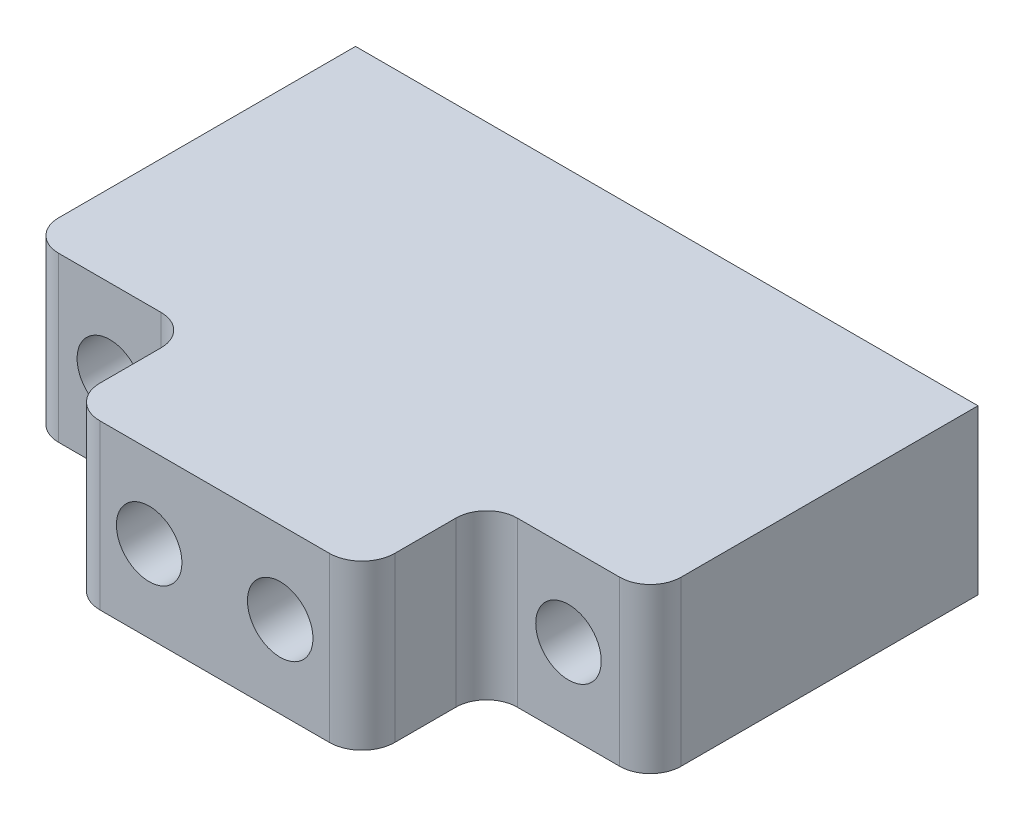
SolidWorks part; units mm, degrees
ref_plane "Front Plane" through (0, 0, 0) normal (0, 0, 1) x (1, 0, 0)
ref_plane "Top Plane" through (0, 0, 0) normal (0, 1, 0) x (1, 0, 0)
ref_plane "Right Plane" through (0, 0, 0) normal (1, 0, 0) x (0, 0, -1)
sketch "Sketch1" plane through (0, 0, 0) normal (0, 0, 1) x (1, 0, 0)
  line L0 (-24.13, 0) -> (-17.78, 0) construction
  line L1 (-24.13, 6.35) -> (24.13, 6.35)
  line L2 (-24.13, 6.35) -> (-24.13, -6.35)
  line L3 (-24.13, -6.35) -> (24.13, -6.35)
  line L4 (24.13, 6.35) -> (24.13, -6.35)
  line L5 (-24.13, 6.35) -> (24.13, -6.35) construction
  line L6 (-24.13, -6.35) -> (24.13, 6.35) construction
  circle A0 centre (-17.78, 0) radius 2.54
  point P0 (0, 0)
  dimension "D3" = 6.35
  dimension "D1" = 48.26
  dimension "D2" = 12.7
extrude "Boss-Extrude2" add sketch "Sketch1" against normal blind 5.08
sketch "Sketch3" plane through (0, 0, 0) normal (0, 0, 1) x (1, 0, 0)
  line L0 (24.13, 0) -> (17.78, 0) construction
  line L1 (24.13, -6.35) -> (24.13, 6.35) construction
  circle A0 centre (17.78, 0) radius 2.54
  dimension "D1" = 6.35
extrude "Cut-Extrude1" cut sketch "Sketch3" against normal through all
sketch "Sketch4" plane through (0, 0, 0) normal (0, 0, 1) x (1, 0, 0)
  line L0 (-24.13, 0) -> (-11.43, 0) construction
  line L1 (-24.13, 6.35) -> (-24.13, -6.35) construction
  line L2 (24.13, 6.35) -> (-24.13, 6.35) construction
  line L3 (-11.43, 6.35) -> (-7.62, 6.35)
  line L4 (-11.43, 6.35) -> (-11.43, -6.35)
  line L5 (-11.43, -6.35) -> (-7.62, -6.35)
  line L6 (-7.62, 6.35) -> (-7.62, -6.35)
  line L7 (-24.13, -6.35) -> (24.13, -6.35) construction
  dimension "D1" = 3.81
  dimension "D2" = 12.7
sketch "Sketch5" plane through (0, 0, 0) normal (0, 0, 1) x (1, 0, 0)
  line L0 (24.13, 0) -> (15.24, 0) construction
  line L1 (24.13, -6.35) -> (24.13, 6.35) construction
  line L2 (15.24, 0) -> (9.525, 0) construction
  line L3 (-24.13, -6.35) -> (24.13, -6.35) construction
  line L4 (7.62, 6.35) -> (11.43, 6.35)
  line L5 (7.62, 6.35) -> (7.62, -6.35)
  line L6 (7.62, -6.35) -> (11.43, -6.35)
  line L7 (11.43, 6.35) -> (11.43, -6.35)
  line L8 (7.62, 6.35) -> (11.43, -6.35) construction
  line L9 (7.62, -6.35) -> (11.43, 6.35) construction
  dimension "D1" = 12.7
  dimension "D3" = 3.81
extrude "Boss-Extrude5" add sketch "Sketch4" along normal blind 27.94 contours L4 L5 L6 L3
extrude "Boss-Extrude6" add sketch "Sketch5" along normal blind 27.94 contours L5 L6 L7 L4
sketch "Sketch7" plane through (0, 0, 27.94) normal (0, 0, 1) x (1, 0, 0)
  line L1 (-11.43, 6.35) -> (11.43, 6.35)
  line L2 (-11.43, 6.35) -> (-11.43, -6.35)
  line L3 (-11.43, -6.35) -> (11.43, -6.35)
  line L4 (11.43, 6.35) -> (11.43, -6.35)
extrude "Boss-Extrude8" add sketch "Sketch7" along normal blind 2.032
sketch "Sketch10" plane through (0, 0, 29.972) normal (0, 0, 1) x (1, 0, 0)
  line L0 (-11.43, 0) -> (-5.08, 0) construction
  line L1 (-11.43, 6.35) -> (-11.43, -6.35) construction
  circle A0 centre (-5.08, 0) radius 2.54
extrude "Cut-Extrude4" cut sketch "Sketch10" against normal blind 2.032
sketch "Sketch11" plane through (0, 0, 29.972) normal (0, 0, 1) x (1, 0, 0)
  line L0 (11.43, 0) -> (5.08, 0) construction
  line L1 (11.43, -6.35) -> (11.43, 6.35) construction
  circle A0 centre (5.08, 0) radius 2.54
extrude "Cut-Extrude5" cut sketch "Sketch11" against normal blind 2.032
fillet "Fillet12" radius 2.54 2 edges at (11.43, 0, 29.972) (-11.43, 0, 29.972)
sketch "Sketch12" plane through (0, 0, 0) normal (0, 0, 1) x (1, 0, 0)
  line L1 (-7.62, 6.35) -> (7.62, 6.35)
  line L2 (-7.62, 6.35) -> (-7.62, -6.35)
  line L3 (-7.62, -6.35) -> (7.62, -6.35)
  line L4 (7.62, 6.35) -> (7.62, -6.35)
  line L5 (-7.62, 6.35) -> (7.62, -6.35) construction
  line L6 (-7.62, -6.35) -> (7.62, 6.35) construction
  point P0 (0, 0)
extrude "Boss-Extrude9" add sketch "Sketch12" along normal up to surface (27.94 mm away) up to face at (0.635, 0, 27.94)
sketch "Sketch13" plane through (0, 0, 27.94) normal (0, 0, 1) x (1, 0, 0)
  circle A0 centre (-5.08, 0) radius 2.54
sketch "Sketch14" plane through (0, 0, 27.94) normal (0, 0, 1) x (1, 0, 0)
  circle A0 centre (5.08, 0) radius 2.54
extrude "Cut-Extrude6" cut sketch "Sketch13" against normal blind 7.493
extrude "Cut-Extrude7" cut sketch "Sketch14" against normal blind 7.493
sketch "Sketch20" plane through (0, 0, -5.08) normal (0, 0, -1) x (-1, 0, 0)
  circle A0 centre (17.78, 0) radius 4.8006
  dimension "D1" = 9.6012
extrude "Cut-Extrude13" cut sketch "Sketch20" against normal blind 3.429
sketch "Sketch21" plane through (0, 0, 0) normal (0, 0, 1) x (1, 0, 0)
  line L1 (-24.13, 6.35) -> (-11.43, 6.35)
  line L2 (-24.13, 6.35) -> (-24.13, -6.35)
  line L3 (-24.13, -6.35) -> (-11.43, -6.35)
  line L4 (-11.43, 6.35) -> (-11.43, -6.35)
extrude "Boss-Extrude10" add sketch "Sketch21" along normal blind 20.32
sketch "Sketch22" plane through (0, 0, 0) normal (0, 0, -1) x (-1, 0, 0)
  circle A0 centre (17.78, 0) radius 2.54
extrude "Cut-Extrude14" cut sketch "Sketch22" against normal blind 20.32
sketch "Sketch23" plane through (0, 0, 0) normal (0, 0, 1) x (1, 0, 0)
  line L1 (11.43, 6.35) -> (24.13, 6.35)
  line L2 (11.43, 6.35) -> (11.43, -6.35)
  line L3 (11.43, -6.35) -> (24.13, -6.35)
  line L4 (24.13, 6.35) -> (24.13, -6.35)
extrude "Boss-Extrude11" add sketch "Sketch23" along normal blind 20.32
sketch "Sketch24" plane through (0, 0, -5.08) normal (0, 0, -1) x (-1, 0, 0)
  circle A0 centre (-17.78, 0) radius 2.54
extrude "Cut-Extrude15" cut sketch "Sketch24" against normal blind 25.4
sketch "Sketch26" plane through (0, 0, -5.08) normal (0, 0, -1) x (-1, 0, 0)
  circle A0 centre (-17.78, 0) radius 4.8006
extrude "Cut-Extrude16" cut sketch "Sketch26" against normal blind 3.429
fillet "Fillet15" radius 2.38 1 edges at (11.43, 0, 20.32)
fillet "Fillet16" radius 2.38 1 edges at (-11.43, 0, 20.32)
fillet "Fillet17" radius 2.38 2 edges at (-24.13, 0, 20.32) (24.13, 0, 20.32)
